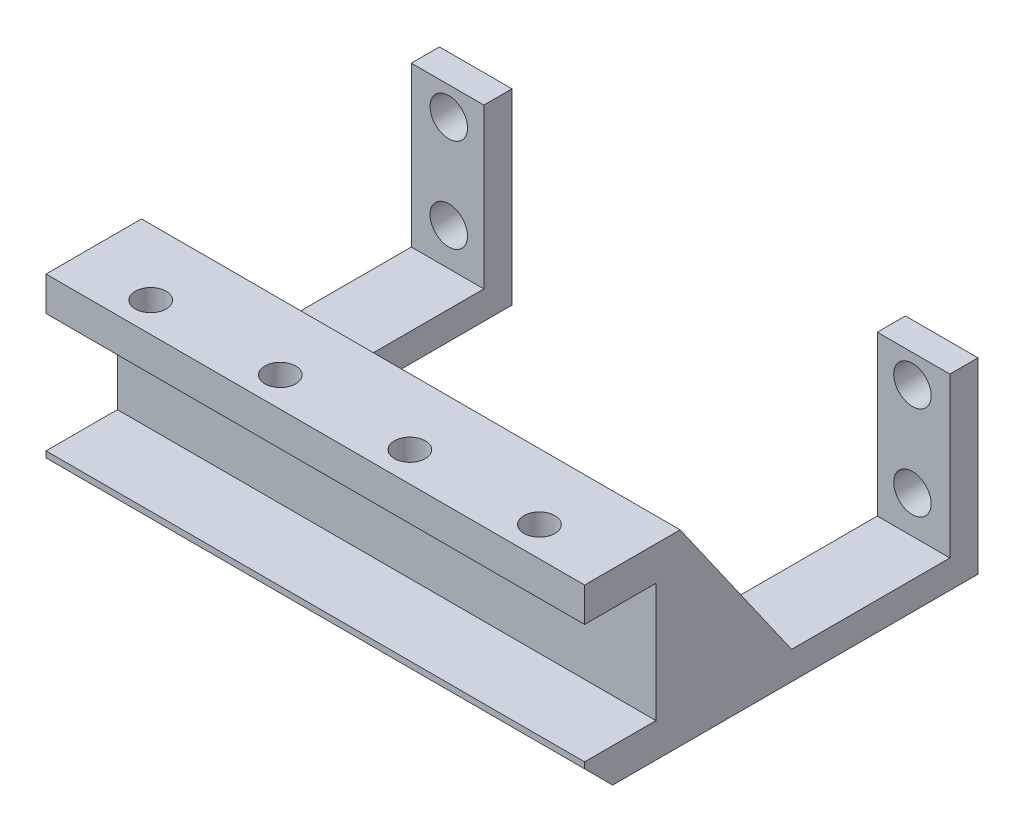
SolidWorks part; units mm, degrees
material "1060 Alloy"
ref_plane "Front Plane" through (0, 0, 0) normal (0, 0, 1) x (1, 0, 0)
ref_plane "Top Plane" through (0, 0, 0) normal (0, 1, 0) x (1, 0, 0)
ref_plane "Right Plane" through (0, 0, 0) normal (1, 0, 0) x (0, 0, -1)
sketch "Sketch1" plane through (0, 0, 0) normal (0, 1, 0) x (1, 0, 0)
  line L1 (0, 0) -> (57.5, 0)
  line L2 (0, 0) -> (0, 42)
  line L3 (0, 42) -> (57.5, 42)
  line L4 (57.5, 0) -> (57.5, 42)
  dimension "D1" = 42
  dimension "D2" = 57.5
extrude "Boss-Extrude1" add sketch "Sketch1" along normal blind 20
sketch "Sketch2" plane through (0, 20, 0) normal (0, 1, 0) x (1, 0, 0)
  line L0 (7.75, 42) -> (7.75, 15.2)
  line L1 (57.5, 42) -> (0, 42) construction
  line L2 (12.75, 10.2) -> (44.75, 10.2)
  line L3 (49.75, 15.2) -> (49.75, 42)
  line L4 (49.75, 42) -> (7.75, 42)
  line L5 (28.75, 10.2) -> (28.75, 0) construction
  line L6 (0, 0) -> (57.5, 0) construction
  arc A0 (7.75, 15.2) -> (12.75, 10.2) centre (12.75, 15.2) ccw
  arc A1 (44.75, 10.2) -> (49.75, 15.2) centre (44.75, 15.2) ccw
  dimension "D3" = 5
  dimension "D1" = 42
  dimension "D2" = 26.8
extrude "Cut-Extrude1" cut sketch "Sketch2" against normal through all
sketch "Sketch3" plane through (57.5, 0, 0) normal (1, 0, 0) x (0, 0, -1)
  line L0 (39, 20) -> (39, 3)
  line L1 (0, 20) -> (42, 20) construction
  line L2 (39, 3) -> (22.1035, 3)
  line L3 (22.1035, 3) -> (10.2, 20)
  line L4 (10.2, 20) -> (39, 20)
  line L5 (10.2, 0) -> (10.2, 20) construction
  line L6 (10.2, 0) -> (10.2, 20) construction
  line L7 (42, 20) -> (42, 0) construction
  dimension "D1" = 17
  dimension "D2" = 3
  dimension "D3" = 35
extrude "Cut-Extrude2" cut sketch "Sketch3" against normal through all
sketch "Sketch4" plane through (0, 0, -42) normal (0, 0, -1) x (-1, 0, 0)
  line L0 (-28.75, 17) -> (-28.75, 20) construction
  line L1 (-53.5, 7) -> (-4, 7) construction
  line L2 (-53.5, 7) -> (-53.5, 17) construction
  line L3 (-53.5, 17) -> (-4, 17) construction
  line L4 (-4, 7) -> (-4, 17) construction
  line L5 (-12.75, 20) -> (-44.75, 20) construction
  circle A0 centre (-53.5, 17) radius 2
  circle A1 centre (-4, 17) radius 2
  circle A2 centre (-4, 7) radius 2
  circle A3 centre (-53.5, 7) radius 2
  dimension "D4" = 4
  dimension "D1" = 10
  dimension "D2" = 49.5
  dimension "D3" = 3
extrude "Cut-Extrude3" cut sketch "Sketch4" against normal up to next
sketch "Sketch5" plane through (57.5, 0, 0) normal (1, 0, 0) x (0, 0, -1)
  line L1 (0, 3.65) -> (7.62, 3.65)
  line L2 (0, 3.65) -> (0, 16.35)
  line L3 (0, 16.35) -> (7.62, 16.35)
  line L4 (7.62, 3.65) -> (7.62, 16.35)
  line L5 (0, 20) -> (0, 0) construction
  point P6 (0, 10)
  point P7 (0, 10)
  dimension "D1" = 7.62
  dimension "D2" = 12.7
extrude "Cut-Extrude4" cut sketch "Sketch5" against normal through all
hole_wizard "M4x0.7 Tapped Hole1" positions "Sketch6" profile "Sketch7" tap size "M4x0.7" standard "ANSI Metric" end condition up to next
sketch "Sketch6" plane through (0, 20, 0) normal (0, 1, 0) x (1, 0, 0)
  line L2 (8, 3.18) -> (21.8333, 3.18) construction
  line L3 (21.8333, 3.18) -> (35.6667, 3.18) construction
  line L4 (35.6667, 3.18) -> (49.5, 3.18) construction
  line L6 (0, 10.2) -> (0, 0) construction
  line L7 (57.5, 0) -> (57.5, 10.2) construction
  line L8 (0, 0) -> (57.5, 0) construction
  point P0 (8, 3.18)
  point P2 (21.8333, 3.18)
  point P4 (35.6667, 3.18)
  point P6 (49.5, 3.18)
  dimension "D1" = 8
  dimension "D2" = 8
  dimension "D3" = 3.18
sketch "Sketch7" plane through (8, 20, -3.18) normal (1, 0, 0) x (0, 0, 1)
  line L0 (0, 0) -> (0, 3.65)
  line L1 (0, 3.65) -> (1.65, 3.65)
  line L2 (1.65, 3.65) -> (1.65, 0)
  line L5 (1.65, 0) -> (0, 0)
  line L11 (0, -6.35) -> (0, 107.95) construction
  dimension "Thru Tap Drill Dia." = 3.3
  dimension "Thru Tap Drill Depth" = 3.65
cosmetic thread "Hole Thread1" parameters "D2"=4
cosmetic thread "Hole Thread2" parameters "D2"=4
cosmetic thread "Hole Thread3" parameters "D2"=4
cosmetic thread "Hole Thread4" parameters "D2"=4
chamfer "Chamfer1" distance 3 angle 45 1 edges at (28.75, 0, 0)
